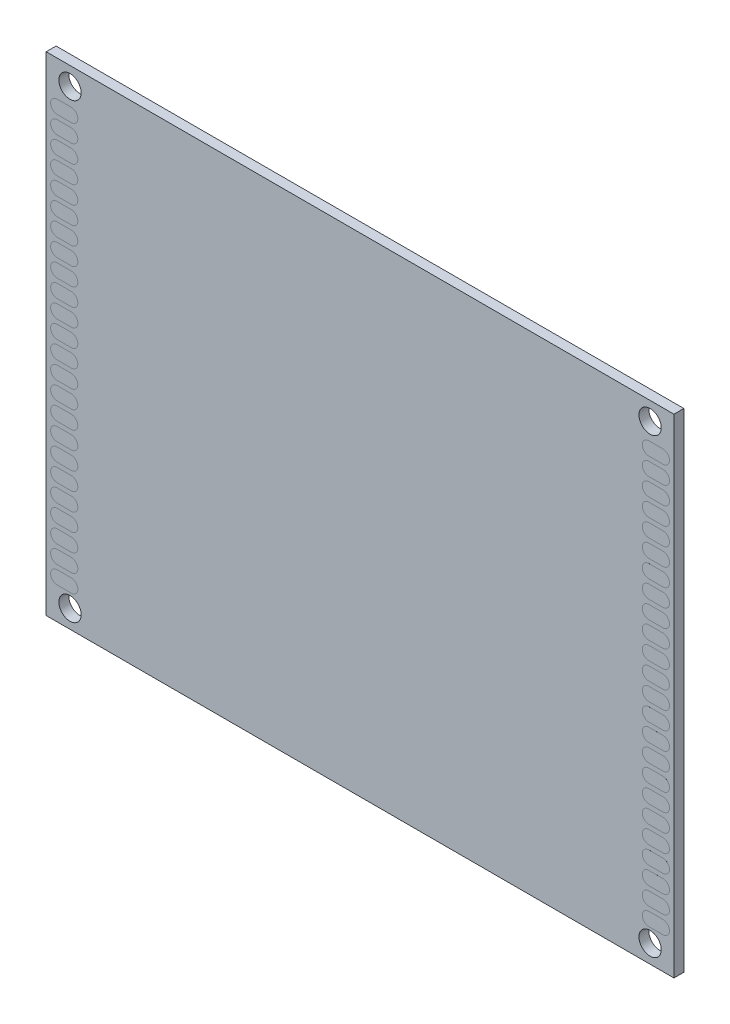
SolidWorks part; units mm, degrees
ref_plane "Front Plane" through (0, 0, 0) normal (0, 0, 1) x (1, 0, 0)
ref_plane "Top Plane" through (0, 0, 0) normal (0, 1, 0) x (1, 0, 0)
ref_plane "Right Plane" through (0, 0, 0) normal (1, 0, 0) x (0, 0, -1)
sketch "Sketch2" plane through (0, 0, 0) normal (0, 0, 1) x (1, 0, 0)
  line L1 (-45, 35) -> (45, 35)
  line L2 (-45, 35) -> (-45, -35)
  line L3 (-45, -35) -> (45, -35)
  line L4 (45, 35) -> (45, -35)
  point P4 (-45, 0)
  point P7 (0, 35)
  dimension "D1" = 90
  dimension "D2" = 70
extrude "Boss-Extrude1" add sketch "Sketch2" along normal mid plane 1.42
sketch "Sketch3" plane through (0, 0, 0) normal (0, 0, 1) x (1, 0, 0)
  line L0 (0, -0.781) -> (0, 0.781) construction
  line L1 (0.781, 0) -> (-0.781, 0) construction
  line L6 (-45, 35) -> (-45, -35) construction
  line L9 (45, 35) -> (-45, 35) construction
  circle A0 centre (-41.58, 32.4) radius 1.6
  circle A1 centre (41.58, 32.4) radius 1.6
  circle A2 centre (41.58, -32.4) radius 1.6
  circle A3 centre (-41.58, -32.4) radius 1.6
  dimension "D1" = 3.2
  dimension "D2" = 1.82
  dimension "D3" = 1
extrude "Cut-Extrude1" cut sketch "Sketch3" against normal through all both and the other way through all
sketch "Sketch4" plane through (0, 0, 0) normal (0, 0, 1) x (1, 0, 0)
  line L0 (-43.41, 28.95) -> (-41.41, 28.95) construction
  line L1 (-43.41, 29.9) -> (-41.41, 29.9)
  line L2 (-43.41, 28) -> (-41.41, 28)
  line L3 (-43.41, 26.41) -> (-41.41, 26.41) construction
  line L4 (-45, 35) -> (-45, -35) construction
  line L5 (-43.41, 27.36) -> (-41.41, 27.36)
  line L6 (-43.41, 25.46) -> (-41.41, 25.46)
  line L7 (-43.41, 23.87) -> (-41.41, 23.87) construction
  line L8 (-43.41, 24.82) -> (-41.41, 24.82)
  line L9 (-43.41, 22.92) -> (-41.41, 22.92)
  line L10 (-43.41, 21.33) -> (-41.41, 21.33) construction
  line L11 (-43.41, 22.28) -> (-41.41, 22.28)
  line L12 (-43.41, 20.38) -> (-41.41, 20.38)
  line L13 (-43.41, 18.79) -> (-41.41, 18.79) construction
  line L14 (-43.41, 19.74) -> (-41.41, 19.74)
  line L15 (-43.41, 17.84) -> (-41.41, 17.84)
  line L16 (-43.41, 16.25) -> (-41.41, 16.25) construction
  line L17 (-43.41, 17.2) -> (-41.41, 17.2)
  line L18 (-43.41, 15.3) -> (-41.41, 15.3)
  line L19 (-43.41, 13.71) -> (-41.41, 13.71) construction
  line L20 (-43.41, 14.66) -> (-41.41, 14.66)
  line L21 (-43.41, 12.76) -> (-41.41, 12.76)
  line L22 (-43.41, 11.17) -> (-41.41, 11.17) construction
  line L23 (-43.41, 12.12) -> (-41.41, 12.12)
  line L24 (-43.41, 10.22) -> (-41.41, 10.22)
  line L25 (-43.41, 8.63) -> (-41.41, 8.63) construction
  line L26 (-43.41, 9.58) -> (-41.41, 9.58)
  line L27 (-43.41, 7.68) -> (-41.41, 7.68)
  line L28 (-43.41, 6.09) -> (-41.41, 6.09) construction
  line L29 (-43.41, 7.04) -> (-41.41, 7.04)
  line L30 (-43.41, 5.14) -> (-41.41, 5.14)
  line L31 (-43.41, 3.55) -> (-41.41, 3.55) construction
  line L32 (-43.41, 4.5) -> (-41.41, 4.5)
  line L33 (-43.41, 2.6) -> (-41.41, 2.6)
  line L34 (-43.41, 1.01) -> (-41.41, 1.01) construction
  line L35 (-43.41, 1.96) -> (-41.41, 1.96)
  line L36 (-43.41, 0.06) -> (-41.41, 0.06)
  line L37 (-43.41, -1.53) -> (-41.41, -1.53) construction
  line L38 (-43.41, -0.58) -> (-41.41, -0.58)
  line L39 (-43.41, -2.48) -> (-41.41, -2.48)
  line L40 (-43.41, -4.07) -> (-41.41, -4.07) construction
  line L41 (-43.41, -3.12) -> (-41.41, -3.12)
  line L42 (-43.41, -5.02) -> (-41.41, -5.02)
  line L43 (-43.41, -6.61) -> (-41.41, -6.61) construction
  line L44 (-43.41, -5.66) -> (-41.41, -5.66)
  line L45 (-43.41, -7.56) -> (-41.41, -7.56)
  line L46 (-43.41, -9.15) -> (-41.41, -9.15) construction
  line L47 (-43.41, -8.2) -> (-41.41, -8.2)
  line L48 (-43.41, -10.1) -> (-41.41, -10.1)
  line L49 (-43.41, -11.69) -> (-41.41, -11.69) construction
  line L50 (-43.41, -10.74) -> (-41.41, -10.74)
  line L51 (-43.41, -12.64) -> (-41.41, -12.64)
  line L52 (-43.41, -14.23) -> (-41.41, -14.23) construction
  line L53 (-43.41, -13.28) -> (-41.41, -13.28)
  line L54 (-43.41, -15.18) -> (-41.41, -15.18)
  line L55 (-43.41, -16.77) -> (-41.41, -16.77) construction
  line L56 (-43.41, -15.82) -> (-41.41, -15.82)
  line L57 (-43.41, -17.72) -> (-41.41, -17.72)
  line L58 (-43.41, -19.31) -> (-41.41, -19.31) construction
  line L59 (-43.41, -18.36) -> (-41.41, -18.36)
  line L60 (-43.41, -20.26) -> (-41.41, -20.26)
  line L61 (-43.41, -21.85) -> (-41.41, -21.85) construction
  line L62 (-43.41, -20.9) -> (-41.41, -20.9)
  line L63 (-43.41, -22.8) -> (-41.41, -22.8)
  line L64 (-43.41, -24.39) -> (-41.41, -24.39) construction
  line L65 (-43.41, -23.44) -> (-41.41, -23.44)
  line L66 (-43.41, -25.34) -> (-41.41, -25.34)
  line L67 (-43.41, -26.93) -> (-41.41, -26.93) construction
  line L68 (-43.41, -25.98) -> (-41.41, -25.98)
  line L69 (-43.41, -27.88) -> (-41.41, -27.88)
  line L70 (-43.41, -29.47) -> (-41.41, -29.47) construction
  line L71 (-43.41, -28.52) -> (-41.41, -28.52)
  line L72 (-43.41, -30.42) -> (-41.41, -30.42)
  arc A0 (-43.41, 29.9) -> (-43.41, 28) centre (-43.41, 28.95) ccw
  arc A1 (-41.41, 28) -> (-41.41, 29.9) centre (-41.41, 28.95) ccw
  circle A2 centre (-41.58, 32.4) radius 1.6 construction
  arc A3 (-43.41, 27.36) -> (-43.41, 25.46) centre (-43.41, 26.41) ccw
  arc A4 (-41.41, 25.46) -> (-41.41, 27.36) centre (-41.41, 26.41) ccw
  arc A5 (-43.41, 24.82) -> (-43.41, 22.92) centre (-43.41, 23.87) ccw
  arc A6 (-41.41, 22.92) -> (-41.41, 24.82) centre (-41.41, 23.87) ccw
  arc A7 (-43.41, 22.28) -> (-43.41, 20.38) centre (-43.41, 21.33) ccw
  arc A8 (-41.41, 20.38) -> (-41.41, 22.28) centre (-41.41, 21.33) ccw
  arc A9 (-43.41, 19.74) -> (-43.41, 17.84) centre (-43.41, 18.79) ccw
  arc A10 (-41.41, 17.84) -> (-41.41, 19.74) centre (-41.41, 18.79) ccw
  arc A11 (-43.41, 17.2) -> (-43.41, 15.3) centre (-43.41, 16.25) ccw
  arc A12 (-41.41, 15.3) -> (-41.41, 17.2) centre (-41.41, 16.25) ccw
  arc A13 (-43.41, 14.66) -> (-43.41, 12.76) centre (-43.41, 13.71) ccw
  arc A14 (-41.41, 12.76) -> (-41.41, 14.66) centre (-41.41, 13.71) ccw
  arc A15 (-43.41, 12.12) -> (-43.41, 10.22) centre (-43.41, 11.17) ccw
  arc A16 (-41.41, 10.22) -> (-41.41, 12.12) centre (-41.41, 11.17) ccw
  arc A17 (-43.41, 9.58) -> (-43.41, 7.68) centre (-43.41, 8.63) ccw
  arc A18 (-41.41, 7.68) -> (-41.41, 9.58) centre (-41.41, 8.63) ccw
  arc A19 (-43.41, 7.04) -> (-43.41, 5.14) centre (-43.41, 6.09) ccw
  arc A20 (-41.41, 5.14) -> (-41.41, 7.04) centre (-41.41, 6.09) ccw
  arc A21 (-43.41, 4.5) -> (-43.41, 2.6) centre (-43.41, 3.55) ccw
  arc A22 (-41.41, 2.6) -> (-41.41, 4.5) centre (-41.41, 3.55) ccw
  arc A23 (-43.41, 1.96) -> (-43.41, 0.06) centre (-43.41, 1.01) ccw
  arc A24 (-41.41, 0.06) -> (-41.41, 1.96) centre (-41.41, 1.01) ccw
  arc A25 (-43.41, -0.58) -> (-43.41, -2.48) centre (-43.41, -1.53) ccw
  arc A26 (-41.41, -2.48) -> (-41.41, -0.58) centre (-41.41, -1.53) ccw
  arc A27 (-43.41, -3.12) -> (-43.41, -5.02) centre (-43.41, -4.07) ccw
  arc A28 (-41.41, -5.02) -> (-41.41, -3.12) centre (-41.41, -4.07) ccw
  arc A29 (-43.41, -5.66) -> (-43.41, -7.56) centre (-43.41, -6.61) ccw
  arc A30 (-41.41, -7.56) -> (-41.41, -5.66) centre (-41.41, -6.61) ccw
  arc A31 (-43.41, -8.2) -> (-43.41, -10.1) centre (-43.41, -9.15) ccw
  arc A32 (-41.41, -10.1) -> (-41.41, -8.2) centre (-41.41, -9.15) ccw
  arc A33 (-43.41, -10.74) -> (-43.41, -12.64) centre (-43.41, -11.69) ccw
  arc A34 (-41.41, -12.64) -> (-41.41, -10.74) centre (-41.41, -11.69) ccw
  arc A35 (-43.41, -13.28) -> (-43.41, -15.18) centre (-43.41, -14.23) ccw
  arc A36 (-41.41, -15.18) -> (-41.41, -13.28) centre (-41.41, -14.23) ccw
  arc A37 (-43.41, -15.82) -> (-43.41, -17.72) centre (-43.41, -16.77) ccw
  arc A38 (-41.41, -17.72) -> (-41.41, -15.82) centre (-41.41, -16.77) ccw
  arc A39 (-43.41, -18.36) -> (-43.41, -20.26) centre (-43.41, -19.31) ccw
  arc A40 (-41.41, -20.26) -> (-41.41, -18.36) centre (-41.41, -19.31) ccw
  arc A41 (-43.41, -20.9) -> (-43.41, -22.8) centre (-43.41, -21.85) ccw
  arc A42 (-41.41, -22.8) -> (-41.41, -20.9) centre (-41.41, -21.85) ccw
  arc A43 (-43.41, -23.44) -> (-43.41, -25.34) centre (-43.41, -24.39) ccw
  arc A44 (-41.41, -25.34) -> (-41.41, -23.44) centre (-41.41, -24.39) ccw
  arc A45 (-43.41, -25.98) -> (-43.41, -27.88) centre (-43.41, -26.93) ccw
  arc A46 (-41.41, -27.88) -> (-41.41, -25.98) centre (-41.41, -26.93) ccw
  arc A47 (-43.41, -28.52) -> (-43.41, -30.42) centre (-43.41, -29.47) ccw
  arc A48 (-41.41, -30.42) -> (-41.41, -28.52) centre (-41.41, -29.47) ccw
  point P2 (-42.41, 28.95)
  point P15 (-42.41, 26.41)
  point P22 (-42.41, 23.87)
  point P29 (-42.41, 21.33)
  point P36 (-42.41, 18.79)
  point P43 (-42.41, 16.25)
  point P50 (-42.41, 13.71)
  point P57 (-42.41, 11.17)
  point P64 (-42.41, 8.63)
  point P71 (-42.41, 6.09)
  point P78 (-42.41, 3.55)
  point P85 (-42.41, 1.01)
  point P92 (-42.41, -1.53)
  point P99 (-42.41, -4.07)
  point P106 (-42.41, -6.61)
  point P113 (-42.41, -9.15)
  point P120 (-42.41, -11.69)
  point P127 (-42.41, -14.23)
  point P134 (-42.41, -16.77)
  point P141 (-42.41, -19.31)
  point P148 (-42.41, -21.85)
  point P155 (-42.41, -24.39)
  point P162 (-42.41, -26.93)
  point P169 (-42.41, -29.47)
  dimension "D2" = 3.9
  dimension "D3" = 0.64
  dimension "D4" = 0.9
  dimension "D1" = 1.9
  dimension "D6" = 0.64
  dimension "D5" = 24
extrude "Boss-Extrude2" add sketch "Sketch4" along normal offset from surface 0.0001 and the other way offset from surface (0.711 mm away) 0.001 contours L2 A1 L1 A0 | L6 A4 L5 A3 | L9 A6 L8 A5 | L12 A8 L11 A7 | L15 A10 L14 A9 | L18 A12 L17 A11 | L21 A14 L20 A13 | L24 A16 L23 A15 | L27 A18 L26 A17 | L30 A20 L29 A19 | L33 A22 L32 A21 | L36 A24 L35 A23 | L39 A26 L38 A25 | L42 A28 L41 A27 | L45 A30 L44 A29 | L48 A32 L47 A31 | L51 A34 L50 A33 | L54 A36 L53 A35 | L57 A38 L56 A37 | L60 A40 L59 A39 | L63 A42 L62 A41 | L66 A44 L65 A43 | L69 A46 L68 A45 | L72 A48 L71 A47 up to face at (-43.18, -32.4, 0.71) offset beyond the face yes other way up to face at (-43.18, -32.4, -0.71)
mirror "Mirror1" about plane through (0, 0, 0) normal (1, 0, 0) of "Boss-Extrude2"
